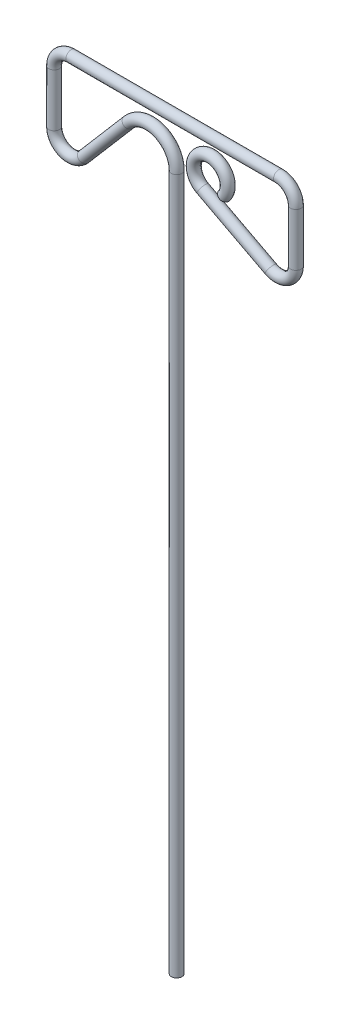
SolidWorks part; units mm, degrees
ref_plane "Front Plane" through (0, 0, 0) normal (0, 0, 1) x (1, 0, 0)
ref_plane "Top Plane" through (0, 0, 0) normal (0, 1, 0) x (1, 0, 0)
ref_plane "Right Plane" through (0, 0, 0) normal (1, 0, 0) x (0, 0, -1)
sketch "Sketch1" plane through (0, 0, 0) normal (0, 0, 1) x (1, 0, 0)
  line L0 (0, 0) -> (0, 113) construction
  line L1 (0, 113) -> (-18, 92) construction
  line L2 (-18, 92) -> (-18, 109) construction
  line L4 (17.5, 92) -> (17.5, 109) construction
  line L5 (-18, 109) -> (17.5, 109) construction
  line L6 (0, 0) -> (0, 102.187)
  line L7 (-7.037, 104.7901) -> (-13.6019, 97.1312)
  line L8 (-18, 98.7581) -> (-18, 106.5)
  line L9 (-15.5, 109) -> (15, 109)
  line L10 (17.5, 106.5) -> (17.5, 98.7581)
  line L11 (13.8393, 96.5439) -> (3.8393, 101.7858)
  circle A0 centre (5, 104) radius 2.5 construction
  circle A1 centre (-4, 102.187) radius 4 construction
  circle A2 centre (-15.5, 98.7581) radius 2.5 construction
  circle A3 centre (15, 98.7581) radius 2.5 construction
  circle A4 centre (-15.5, 106.5) radius 2.5 construction
  circle A5 centre (15, 106.5) radius 2.5 construction
  arc A6 (0, 102.187) -> (-7.037, 104.7901) centre (-4, 102.187) ccw
  arc A7 (-13.6019, 97.1312) -> (-18, 98.7581) centre (-15.5, 98.7581) cw
  arc A8 (-18, 106.5) -> (-15.5, 109) centre (-15.5, 106.5) cw
  arc A9 (15, 109) -> (17.5, 106.5) centre (15, 106.5) cw
  arc A10 (17.5, 98.7581) -> (13.8393, 96.5439) centre (15, 98.7581) cw
  arc A11 (3.8393, 101.7858) -> (7, 102.5) centre (5, 104) cw
  point P3 (10, 105.5264)
  point P32 (0, 0)
  point P34 (0, 0)
  point P35 (0, 0)
  point P37 (0, 0)
  point P38 (0, 0)
  point P40 (0, 0)
  point P41 (0, 0)
  point P44 (0, 0)
  point P45 (0, 113)
  point P46 (0, 0)
  point P47 (0, 0)
  point P48 (10, 105.5264)
  point P49 (10, 103.8076)
  point P50 (10, 103.8076)
  point P51 (4.9182, 104.1539)
  point P52 (5.0631, 103.9729)
  point P53 (0, 0)
  point P54 (0, 0)
  point P55 (13.2321, 97.1312)
  dimension "D6" = 5
  dimension "D7" = 8
  dimension "D1" = 113
  dimension "D2" = 18
  dimension "D3" = 21
  dimension "D4" = 17
  dimension "D5" = 15
  dimension "D8" = 5
  dimension "D9" = 5
  dimension "D10" = 2
sketch "Sketch2" plane through (0, 0, 0) normal (0, 1, 0) x (1, 0, 0)
  circle A0 centre (0, 0) radius 0.78
  dimension "D1" = 1.56
sweep "Sweep2" add profiles "Sketch2" path "Sketch1"
